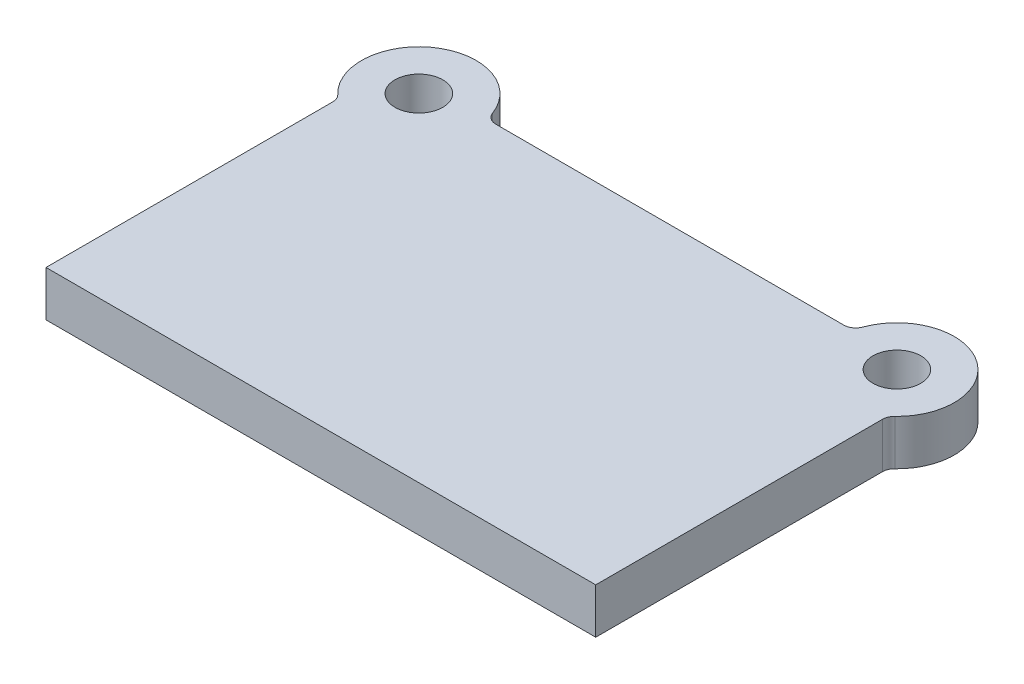
SolidWorks part; units mm, degrees
ref_plane "Front Plane" through (0, 0, 0) normal (0, 0, 1) x (1, 0, 0)
ref_plane "Top Plane" through (0, 0, 0) normal (0, 1, 0) x (1, 0, 0)
ref_plane "Right Plane" through (0, 0, 0) normal (1, 0, 0) x (0, 0, -1)
sketch "Sketch1" plane through (0, 0, 0) normal (0, 1, 0) x (1, 0, 0)
  line L0 (230, 0) -> (-230, 0)
  line L1 (-230, 0) -> (-230, 244.53)
  line L2 (0, 0) -> (0, 292) construction
  line L3 (153.0532, 292) -> (-153.0532, 292)
  line L4 (230, 0) -> (230, 244.53)
  arc A0 (-153.0532, 292) -> (-230, 244.53) centre (-200, 282) ccw
  circle A1 centre (-200, 282) radius 20
  circle A2 centre (200, 282) radius 20
  arc A3 (153.0532, 292) -> (230, 244.53) centre (200, 282) cw
  point P9 (-172.2353, 302.8235)
  point P10 (-206.7878, 269.505)
  point P11 (-134.4854, 332.4706)
  dimension "D1" = 96
  dimension "D2" = 40
  dimension "D3" = 282
  dimension "D4" = 292
  dimension "D5" = 460
  dimension "D6" = 400
extrude "Boss-Extrude1" add sketch "Sketch1" along normal blind 38
fillet "Fillet1" radius 10 4 edges at (153.0532, 19, -292) (-230, 19, -244.53) (-153.0532, 19, -292) (230, 19, -244.53)
